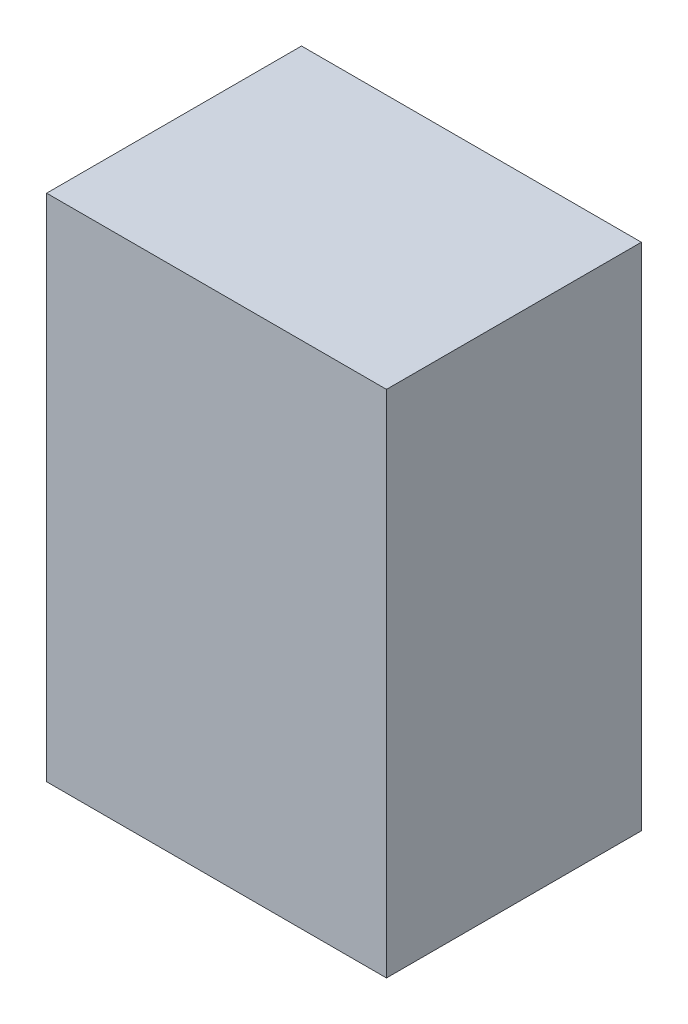
SolidWorks part; units mm, degrees
ref_plane "Front Plane" through (0, 0, 0) normal (0, 0, 1) x (1, 0, 0)
ref_plane "Top Plane" through (0, 0, 0) normal (0, 1, 0) x (1, 0, 0)
ref_plane "Right Plane" through (0, 0, 0) normal (1, 0, 0) x (0, 0, -1)
sketch "Sketch1" plane through (0, 0, 0) normal (0, 1, 0) x (1, 0, 0)
  line L1 (0, 0) -> (-80, 0)
  line L2 (0, 0) -> (0, 60)
  line L3 (0, 60) -> (-80, 60)
  line L4 (-80, 0) -> (-80, 60)
  dimension "D1" = 60
  dimension "D2" = 80
extrude "Extrude1" add sketch "Sketch1" along normal blind 120
